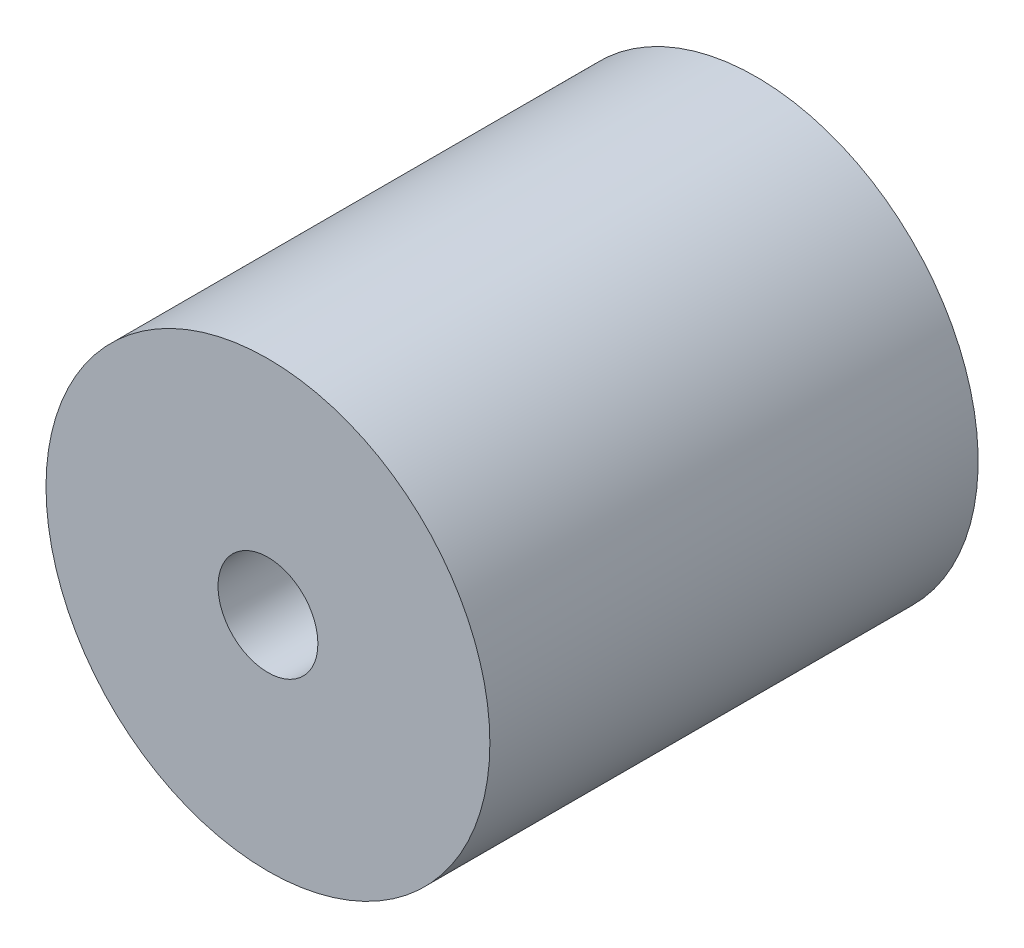
SolidWorks part; units mm, degrees
ref_plane "Plano frontal" through (0, 0, 0) normal (0, 0, 1) x (1, 0, 0)
ref_plane "Plano superior" through (0, 0, 0) normal (0, 1, 0) x (1, 0, 0)
ref_plane "Plano direito" through (0, 0, 0) normal (1, 0, 0) x (0, 0, -1)
sketch "Esboço1" plane through (0, 0, 0) normal (0, 0, 1) x (1, 0, 0)
  circle A0 centre (0, 0) radius 10
  circle A1 centre (0, 0) radius 2.25
extrude "Ressalto-extrusão1" add sketch "Esboço1" along normal blind 15
sketch "Esboço2" plane through (0, 0, 0) normal (1, 0, 0) x (0, 0, -1)
  line L0 (0, 0) -> (-15, 0) construction
  line L1 (-15, 10) -> (-15, -10) construction
  circle A0 centre (-7.5, 0) radius 2
  dimension "D1" = 4
extrude "Corte-extrusão1" cut sketch "Esboço2" against normal blind 10
sketch "Esboço3" plane through (0, 0, 0) normal (0, 0, -1) x (-1, 0, 0)
  circle A0 centre (0, 0) radius 10
  circle A1 centre (0, 7.1) radius 0.5477
  circle A2 centre (7.1, 0) radius 0.5477
  circle A3 centre (0, -7.1) radius 0.5477
  circle A4 centre (-7.1, 0) radius 0.5477
  circle A5 centre (0, 0) radius 3.7
  point P14 (0, 0)
  dimension "D1" = 7.1
  dimension "D2" = 4
extrude "Ressalto-extrusão2" add sketch "Esboço3" along normal blind 7
